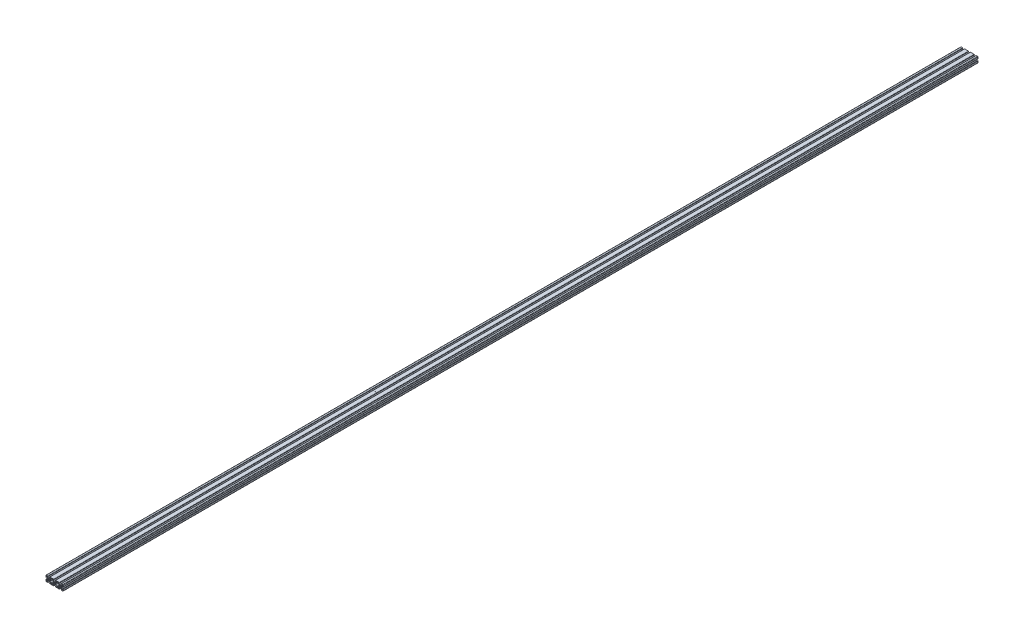
SolidWorks part; units mm, degrees
material "6061 Alloy"
ref_plane "Front Plane" through (0, 0, 0) normal (0, 0, 1) x (1, 0, 0)
ref_plane "Top Plane" through (0, 0, 0) normal (0, 1, 0) x (1, 0, 0)
ref_plane "Right Plane" through (0, 0, 0) normal (1, 0, 0) x (0, 0, -1)
sketch "Sketch2" plane through (0, 0, 0) normal (0, 0, 1) x (1, 0, 0)
  line L0 (-31.4282, -10.36) -> (-29.32, -10.36)
  line L1 (-6.4282, -10.36) -> (-4.32, -10.36)
  line L2 (-7.1366, -8.6498) -> (-3.8133, -5.3265)
  line L3 (-1.5765, -4.4) -> (1.5765, -4.4)
  line L4 (7.1366, -8.6498) -> (3.8133, -5.3265)
  line L5 (4.32, -10.36) -> (6.4282, -10.36)
  line L6 (-19.6735, 3.8133) -> (-16.35, 7.1363)
  line L7 (-20.6, -1.5765) -> (-20.6, 1.5765)
  line L8 (-16.3303, -7.1166) -> (-19.6735, -3.8133)
  line L9 (-8.7995, -7.3028) -> (-5.3476, -3.8509)
  line L10 (-4.421, 1.5389) -> (-4.421, -1.614)
  line L11 (-8.7421, 7.1704) -> (-5.3476, 3.7758)
  line L12 (8.7421, 7.1704) -> (5.3476, 3.7758)
  line L13 (9.6706, 9.4119) -> (9.6706, 9.5983)
  line L14 (10.461, 10.36) -> (14.6679, 10.36)
  line L15 (15.4301, 9.5978) -> (15.4301, 9.4119)
  line L16 (16.35, 7.1363) -> (19.6735, 3.8133)
  line L17 (20.6, -1.5765) -> (20.6, 1.5765)
  line L18 (4.421, 1.5389) -> (4.421, -1.614)
  line L19 (5.3476, -3.8509) -> (8.7995, -7.3028)
  line L20 (9.728, -9.6553) -> (9.728, -9.5443)
  line L21 (15.4018, -9.3582) -> (15.4018, -9.6574)
  line L22 (10.4902, -10.4175) -> (14.6971, -10.4175)
  line L23 (16.3303, -7.1166) -> (19.6735, -3.8133)
  line L24 (35.36, 6.4282) -> (35.36, 4.32)
  line L25 (37.5, 4.32) -> (37.5, 9.2154)
  line L26 (37.5, 9.2154) -> (37.5, 10.5352)
  line L27 (35.5352, 12.5) -> (29.5148, 12.5)
  line L28 (-35.5352, 12.5) -> (-29.32, 12.5)
  line L29 (29.5148, 10.36) -> (31.4282, 10.36)
  line L30 (32.1366, 8.6498) -> (28.8133, 5.3265)
  line L31 (26.5765, 4.4) -> (23.4235, 4.4)
  line L32 (17.8634, 8.6498) -> (21.1867, 5.3265)
  line L33 (18.5718, 10.36) -> (20.4852, 10.36)
  line L34 (4.32, 12.5) -> (20.4852, 12.5)
  line L35 (-20.68, 12.5) -> (-4.32, 12.5)
  line L36 (-25, 0) -> (-25, -17.6054) construction
  line L37 (4.32, 10.36) -> (6.4282, 10.36)
  line L38 (7.1366, 8.6498) -> (3.8133, 5.3265)
  line L39 (-1.5765, 4.4) -> (1.5765, 4.4)
  line L40 (-7.1366, 8.6498) -> (-3.8133, 5.3265)
  line L41 (-6.4282, 10.36) -> (-4.32, 10.36)
  line L42 (25, 0) -> (25, -17.6054) construction
  line L43 (35.5352, 10.5352) -> (25, 0) construction
  line L44 (-14.6971, -10.4175) -> (-10.4902, -10.4175)
  line L45 (-20.68, 10.36) -> (-18.5718, 10.36)
  line L46 (-17.8984, 8.6164) -> (-21.6383, 5.2212)
  line L47 (-26.5765, 4.4) -> (-23.7647, 4.4)
  line L48 (-32.1366, 8.6498) -> (-28.8133, 5.3265)
  line L49 (-31.4282, 10.36) -> (-29.32, 10.36)
  line L50 (-20.68, -10.36) -> (-18.5718, -10.36)
  line L51 (18.5718, -10.36) -> (20.4852, -10.36)
  line L52 (-37.5, 10.5352) -> (-37.5, 9.2154)
  line L53 (-37.5, 4.32) -> (-37.5, 9.291)
  line L54 (-35.36, 4.32) -> (-35.36, 6.4282)
  line L55 (-33.6498, 7.1366) -> (-30.3265, 3.8133)
  line L56 (-29.4, 1.5794) -> (-29.4, -1.5765)
  line L57 (-30.3265, -3.8133) -> (-33.6498, -7.1366)
  line L58 (-35.36, -6.4282) -> (-35.36, -4.32)
  line L59 (-37.5, -10.5352) -> (-37.5, -4.32)
  line L60 (-26.6112, -4.4) -> (-23.4235, -4.4)
  line L61 (-35.5352, -12.5) -> (-29.32, -12.5)
  line L62 (-20.68, -12.5) -> (-4.32, -12.5)
  line L63 (-32.1366, -8.6498) -> (-29.1088, -5.622)
  line L64 (-14.6679, 10.36) -> (-10.461, 10.36)
  line L65 (35.36, -6.4282) -> (35.36, -4.32)
  line L66 (-21.1867, -5.3265) -> (-17.8634, -8.6498)
  line L67 (37.5, -10.5352) -> (37.5, -4.32)
  line L68 (4.32, -12.5) -> (20.6719, -12.5)
  line L69 (37.5, -10.5352) -> (37.5, -4.32)
  line L70 (-15.4018, -9.3582) -> (-15.4018, -9.6574)
  line L71 (-9.728, -9.6553) -> (-9.728, -9.5443)
  line L72 (-15.4301, 9.5978) -> (-15.4301, 9.4119)
  line L73 (17.8634, -8.6498) -> (21.1867, -5.3265)
  line L74 (-9.6706, 9.4119) -> (-9.6706, 9.5983)
  line L75 (35.5352, -12.5) -> (29.3281, -12.5)
  line L81 (23.4235, -4.4) -> (26.5765, -4.4)
  line L82 (28.8133, -5.3265) -> (32.1366, -8.6498)
  line L83 (31.4282, -10.36) -> (29.5148, -10.36)
  line L89 (33.6498, -7.1366) -> (30.3265, -3.8133)
  line L90 (29.4, -1.5765) -> (29.4, 1.5765)
  line L91 (30.3265, 3.8133) -> (33.6498, 7.1366)
  line L92 (0, 0) -> (0, 23.2435) construction
  line L93 (0, 0) -> (44.5547, 0) construction
  arc A0 (-6.4282, -10.36) -> (-7.1366, -8.6498) centre (-6.4282, -9.3582) cw
  arc A1 (-3.8133, -5.3265) -> (-1.5765, -4.4) centre (-1.5765, -7.5634) cw
  arc A2 (1.5765, -4.4) -> (3.8133, -5.3265) centre (1.5765, -7.5634) cw
  arc A3 (7.1366, -8.6498) -> (6.4282, -10.36) centre (6.4282, -9.3582) cw
  arc A4 (-20.6, 1.5765) -> (-19.6735, 3.8133) centre (-17.4366, 1.5765) cw
  arc A5 (-19.6735, -3.8133) -> (-20.6, -1.5765) centre (-17.4366, -1.5765) cw
  arc A6 (-4.421, -1.614) -> (-5.3476, -3.8509) centre (-7.5845, -1.614) cw
  arc A7 (-5.3476, 3.7758) -> (-4.421, 1.5389) centre (-7.5845, 1.5389) cw
  arc A8 (-9.728, -9.6553) -> (-10.4902, -10.4175) centre (-10.4902, -9.6553) cw
  arc A9 (-14.6971, -10.4175) -> (-15.4018, -9.6574) centre (-14.6396, -9.6574) cw
  arc A10 (-9.728, -9.5443) -> (-8.7995, -7.3028) centre (-6.558, -9.5443) cw
  arc A11 (-16.3303, -7.1166) -> (-15.4018, -9.3582) centre (-18.5718, -9.3582) cw
  circle A12 centre (25, 0) radius 2.5
  circle A13 centre (0, 0) radius 2.5
  circle A14 centre (-25, 0) radius 2.5
  arc A15 (5.3476, 3.7758) -> (4.421, 1.5389) centre (7.5845, 1.5389) ccw
  arc A16 (8.7421, 7.1704) -> (9.6706, 9.4119) centre (6.5006, 9.4119) ccw
  arc A17 (10.461, 10.36) -> (9.6706, 9.5983) centre (10.4328, 9.5983) ccw
  arc A18 (15.4301, 9.5978) -> (14.6679, 10.36) centre (14.6679, 9.5978) ccw
  arc A19 (15.4301, 9.4119) -> (16.35, 7.1363) centre (18.5718, 9.3582) ccw
  arc A20 (20.6, 1.5765) -> (19.6735, 3.8133) centre (17.4366, 1.5765) ccw
  arc A21 (19.6735, -3.8133) -> (20.6, -1.5765) centre (17.4366, -1.5765) ccw
  arc A22 (16.3303, -7.1166) -> (15.4018, -9.3582) centre (18.5718, -9.3582) ccw
  arc A23 (4.421, -1.614) -> (5.3476, -3.8509) centre (7.5845, -1.614) ccw
  arc A24 (9.728, -9.5443) -> (8.7995, -7.3028) centre (6.558, -9.5443) ccw
  arc A25 (35.36, 4.32) -> (37.5, 4.32) centre (36.43, 4.32) ccw
  arc A26 (37.5, 10.5352) -> (35.5352, 12.5) centre (35.5352, 10.5352) ccw
  arc A27 (29.5148, 12.5) -> (29.5148, 10.36) centre (29.5148, 11.43) ccw
  arc A28 (32.1366, 8.6498) -> (31.4282, 10.36) centre (31.4282, 9.3582) ccw
  arc A29 (26.5765, 4.4) -> (28.8133, 5.3265) centre (26.5765, 7.5634) ccw
  arc A30 (21.1867, 5.3265) -> (23.4235, 4.4) centre (23.4235, 7.5634) ccw
  arc A31 (18.5718, 10.36) -> (17.8634, 8.6498) centre (18.5718, 9.3582) ccw
  arc A32 (20.4852, 10.36) -> (20.4852, 12.5) centre (20.4852, 11.43) ccw
  arc A33 (4.32, 12.5) -> (4.32, 10.36) centre (4.32, 11.43) ccw
  arc A34 (7.1366, 8.6498) -> (6.4282, 10.36) centre (6.4282, 9.3582) ccw
  arc A35 (1.5765, 4.4) -> (3.8133, 5.3265) centre (1.5765, 7.5634) ccw
  arc A36 (-3.8133, 5.3265) -> (-1.5765, 4.4) centre (-1.5765, 7.5634) ccw
  arc A37 (-6.4282, 10.36) -> (-7.1366, 8.6498) centre (-6.4282, 9.3582) ccw
  arc A38 (-4.32, 10.36) -> (-4.32, 12.5) centre (-4.32, 11.43) ccw
  arc A39 (-20.68, 12.5) -> (-20.68, 10.36) centre (-20.68, 11.43) ccw
  arc A40 (-17.8984, 8.6164) -> (-18.5718, 10.36) centre (-18.5718, 9.3582) ccw
  arc A41 (-23.7647, 4.4) -> (-21.6383, 5.2212) centre (-23.7647, 7.5634) ccw
  arc A42 (-28.8133, 5.3265) -> (-26.5765, 4.4) centre (-26.5765, 7.5634) ccw
  arc A43 (-31.4282, 10.36) -> (-32.1366, 8.6498) centre (-31.4282, 9.3582) ccw
  arc A44 (-29.32, 10.36) -> (-29.32, 12.5) centre (-29.32, 11.43) ccw
  arc A45 (-35.5352, 12.5) -> (-37.5, 10.5352) centre (-35.5352, 10.5352) ccw
  arc A46 (-37.5, 4.32) -> (-35.36, 4.32) centre (-36.43, 4.32) ccw
  arc A47 (-33.6498, 7.1366) -> (-35.36, 6.4282) centre (-34.3582, 6.4282) ccw
  arc A48 (-29.4, 1.5794) -> (-30.3265, 3.8133) centre (-32.5634, 1.5765) ccw
  arc A49 (-30.3265, -3.8133) -> (-29.4, -1.5765) centre (-32.5634, -1.5765) ccw
  arc A50 (-35.36, -6.4282) -> (-33.6498, -7.1366) centre (-34.3582, -6.4282) ccw
  arc A51 (-35.36, -4.32) -> (-37.5, -4.32) centre (-36.43, -4.32) ccw
  arc A52 (-37.5, -10.5352) -> (-35.5352, -12.5) centre (-35.5352, -10.5352) ccw
  arc A53 (-29.32, -12.5) -> (-29.32, -10.36) centre (-29.32, -11.43) ccw
  arc A54 (-32.1366, -8.6498) -> (-31.4282, -10.36) centre (-31.4282, -9.3582) ccw
  arc A55 (-26.6112, -4.4) -> (-29.1088, -5.622) centre (-26.6112, -7.5634) ccw
  arc A56 (-21.1867, -5.3265) -> (-23.4235, -4.4) centre (-23.4235, -7.5634) ccw
  arc A57 (-18.5718, -10.36) -> (-17.8634, -8.6498) centre (-18.5718, -9.3582) ccw
  arc A58 (-20.68, -10.36) -> (-20.68, -12.5) centre (-20.68, -11.43) ccw
  arc A59 (-4.32, -12.5) -> (-4.3718, -10.36) centre (-4.32, -11.4294) ccw
  arc A60 (-15.4301, 9.4119) -> (-16.35, 7.1363) centre (-18.5718, 9.3582) cw
  arc A61 (-15.4301, 9.5978) -> (-14.6679, 10.36) centre (-14.6679, 9.5978) cw
  arc A62 (-10.461, 10.36) -> (-9.6706, 9.5983) centre (-10.4328, 9.5983) cw
  arc A63 (-8.7421, 7.1704) -> (-9.6706, 9.4119) centre (-6.5006, 9.4119) cw
  arc A64 (4.3718, -10.36) -> (4.32, -12.5) centre (4.32, -11.4294) ccw
  arc A65 (20.6719, -12.5) -> (20.4852, -10.36) centre (20.6719, -11.4219) ccw
  arc A66 (17.8634, -8.6498) -> (18.5718, -10.36) centre (18.5718, -9.3582) ccw
  arc A67 (23.4235, -4.4) -> (21.1867, -5.3265) centre (23.4235, -7.5634) ccw
  arc A68 (28.8133, -5.3265) -> (26.5765, -4.4) centre (26.5765, -7.5634) ccw
  arc A69 (31.4282, -10.36) -> (32.1366, -8.6498) centre (31.4282, -9.3582) ccw
  arc A70 (29.5148, -10.36) -> (29.3281, -12.5) centre (29.3281, -11.4219) ccw
  arc A71 (35.5352, -12.5) -> (37.5, -10.5352) centre (35.5352, -10.5352) ccw
  arc A72 (37.5, -4.32) -> (35.36, -4.32) centre (36.43, -4.32) ccw
  arc A73 (33.6498, -7.1366) -> (35.36, -6.4282) centre (34.3582, -6.4282) ccw
  arc A74 (29.4, -1.5765) -> (30.3265, -3.8133) centre (32.5634, -1.5765) ccw
  arc A75 (30.3265, 3.8133) -> (29.4, 1.5765) centre (32.5634, 1.5765) ccw
  arc A76 (35.36, 6.4282) -> (33.6498, 7.1366) centre (34.3582, 6.4282) ccw
  arc A77 (14.6971, -10.4175) -> (15.4018, -9.6574) centre (14.6396, -9.6574) ccw
  arc A78 (9.728, -9.6553) -> (10.4902, -10.4175) centre (10.4902, -9.6553) ccw
  dimension "D3" = 12.5
  dimension "D4" = 6.5
  dimension "D6" = 3.17
  dimension "D8" = 5
  dimension "D11" = 6.5
  dimension "D12" = 3.17
  dimension "D13" = 3.17
  dimension "D14" = 14.86
  dimension "D16" = 0.7622
  dimension "D7" = 3.1634
  dimension "D10" = 3.1634
  dimension "D15" = 0.7622
  dimension "D17" = 3.1634
  dimension "D18" = 3.17
  dimension "D1" = 75
  dimension "D2" = 25
  dimension "D5" = 2.14
  dimension "D9" = 25
extrude "Extrude1" add sketch "Sketch2" against normal blind 4000
